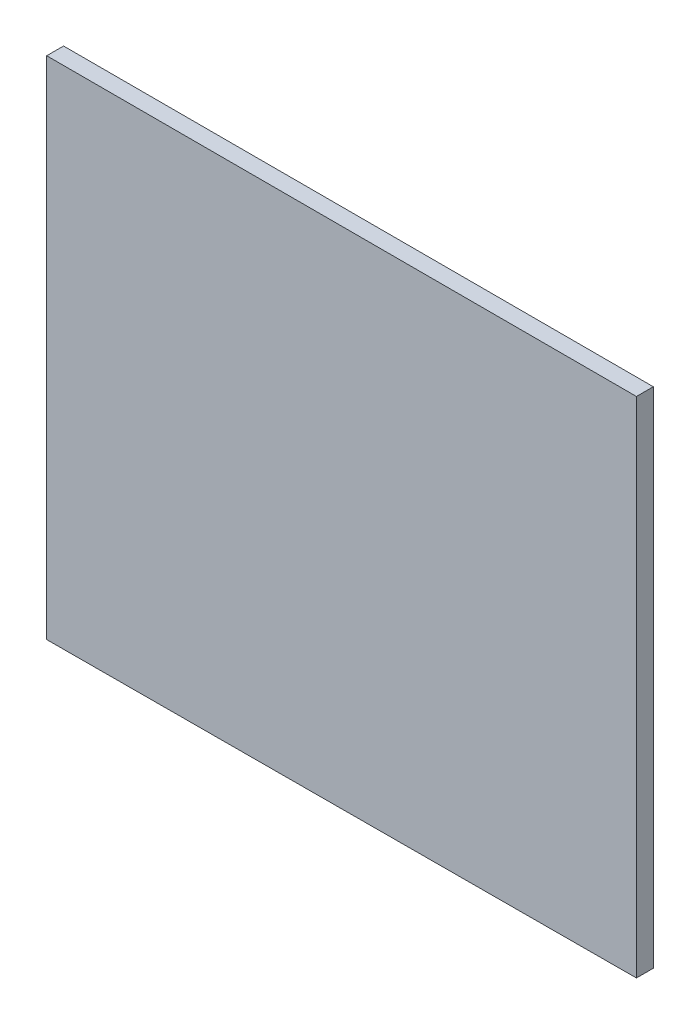
SolidWorks part; units mm, degrees
ref_plane "Alzado" through (0, 0, 0) normal (0, 0, 1) x (1, 0, 0)
ref_plane "Planta" through (0, 0, 0) normal (0, 1, 0) x (1, 0, 0)
ref_plane "Vista lateral" through (0, 0, 0) normal (1, 0, 0) x (0, 0, -1)
sketch "Model" plane through (0, 0, 0) normal (0, 0, 1) x (1, 0, 0)
  line L0 (42.3997, 28.7357) -> (38.901, 28.725)
  line L1 (42.3997, 31.7237) -> (38.901, 31.725)
  line L2 (38.901, 31.725) -> (38.901, 28.725)
  line L3 (42.3997, 28.7357) -> (42.3997, 31.7237)
extrude "Saliente-Extruir1" add sketch "Model" along normal blind 0.1
